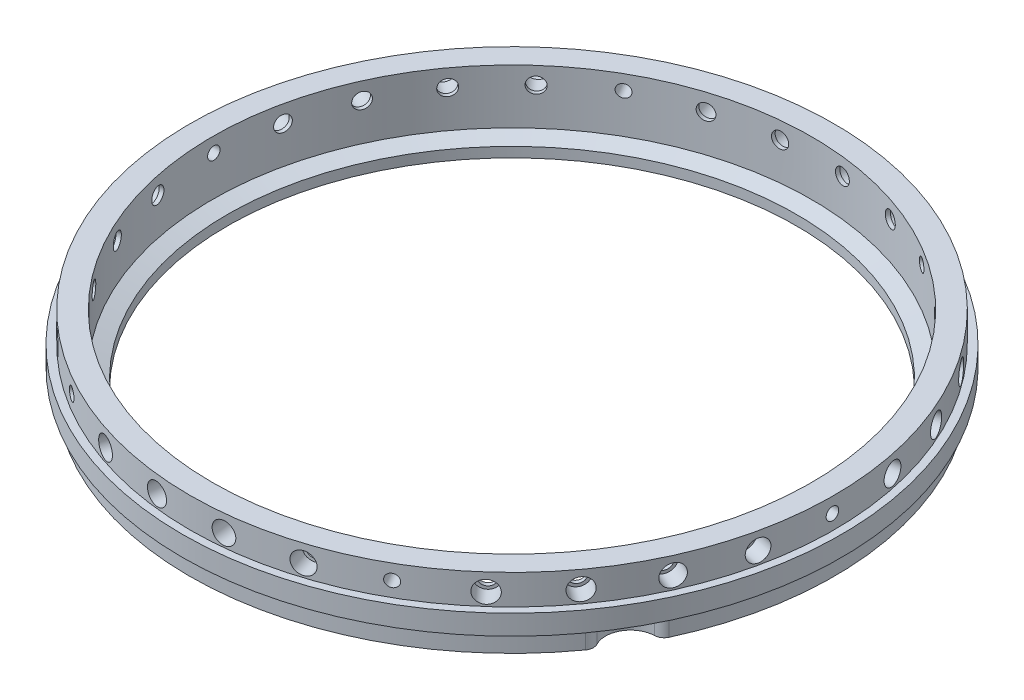
SolidWorks part; units mm, degrees
ref_plane "Front Plane" through (0, 0, 0) normal (0, 0, 1) x (1, 0, 0)
ref_plane "Top Plane" through (0, 0, 0) normal (0, 1, 0) x (1, 0, 0)
ref_plane "Right Plane" through (0, 0, 0) normal (1, 0, 0) x (0, 0, -1)
ref_plane "Plane1" through (0, 0, -36.724) normal (0, 0, 1) x (1, 0, 0)
sketch "Sketch1" plane through (0, 0, -36.724) normal (0, 0, 1) x (1, 0, 0)
  line L0 (122.0725, -167.4149) -> (38.2525, -167.4149)
  line L1 (38.2525, -167.4149) -> (38.2525, -172.4949)
  line L2 (38.2525, -172.4949) -> (122.0725, -172.4949)
  line L3 (122.0725, -172.4949) -> (122.0725, -167.4149)
  line L4 (38.2525, -167.4149) -> (38.2525, -172.4949) construction
revolve "Revolve1" add sketch "Sketch1" angle 360 about L4
sketch "Sketch2" plane through (0, -172.4949, 0) normal (0, -1, 0) x (1, 0, 0)
  arc A0 (-35.7204, -1.3902) -> (-29.763, 9.0403) centre (-34.5321, 4.8476) ccw
  arc A1 (-29.763, 9.0403) -> (105.8389, 9.6716) centre (38.2525, -36.724) cw
  arc A2 (105.8389, 9.6716) -> (111.8933, -0.7029) centre (110.6469, 5.5236) ccw
  arc A3 (111.8933, -0.7029) -> (44.6391, -118.4533) centre (38.2525, -36.724) cw
  arc A4 (44.6391, -118.4533) -> (32.6273, -118.5092) centre (38.6428, -120.5431) ccw
  arc A5 (32.6273, -118.5092) -> (-35.7204, -1.3902) centre (38.2525, -36.724) cw
extrude "Boss-Extrude1" add sketch "Sketch2" along normal blind 5.08
sketch "Sketch3" plane through (0, -167.4149, 0) normal (0, 1, 0) x (-1, 0, 0)
  circle A0 centre (-38.2525, -36.724) radius 81.8896
extrude "Boss-Extrude2" add sketch "Sketch3" along normal blind 7.62
hole_wizard "Hole1" positions "Sketch5" profile "Sketch4" legacy
sketch "Sketch5" plane through (0, -159.7949, 0) normal (0, 1, 0) x (1, 0, 0)
  point P0 (38.2525, 36.724)
sketch "Sketch4" plane through (38.2525, -159.7949, -36.724) normal (1, 0, 0) x (0, 0, 1)
  line L0 (0, 0) -> (0, 17.78)
  line L1 (0, 17.78) -> (72.39, 17.78)
  line L2 (72.39, 17.78) -> (72.39, 15.24)
  line L3 (72.39, 15.24) -> (76.2, 13.8533)
  line L4 (76.2, 13.8533) -> (76.2, 0)
  line L5 (76.2, 0) -> (0, 0)
  line L6 (0, -6.13) -> (0, 109.2824) construction
  line L7 (-72.39, 15.24) -> (-76.2, 13.8533) construction
  line L8 (0, 17.78) -> (-72.39, 17.78) construction
  dimension "Diameter" = 144.78
  dimension "Depth" = 17.78
  dimension "C-Drill Diameter" = 152.4
  dimension "C-Drill Depth" = 13.8533
  dimension "C-Drill Angle" = 140
hole_wizard "CBORE for M3.5 Hex Head Machine Screw1" positions "3DSketch1" profile "Sketch6" counterbore size "M3.5" standard "ANSI Metric"
sketch3d "3DSketch1"
  point P0 (13.3101, -164.1649, -114.7226)
sketch "Sketch6" plane through (13.3101, -164.1649, -114.7226) normal (0, 1, 0) x (-0.9525, 0, 0.3046)
  line L0 (0, 0) -> (0, 5.6896)
  line L1 (0, 5.6896) -> (2, 5.6896)
  line L3 (2, 5.6896) -> (2, 4.6896)
  line L4 (2, 4.6896) -> (2.75, 4.6896)
  line L5 (2.75, 4.6896) -> (2.75, 0)
  line L7 (2.75, 0) -> (0, 0)
  line L11 (0, -6.35) -> (0, 107.95) construction
  dimension "Thru Hole Dia." = 4
  dimension "Thru Hole Depth" = 5.6896
  dimension "C'Bore Dia." = 5.5
  dimension "C'Bore Depth" = 4.6896
hole_wizard "CBORE for M3.5 Hex Head Machine Screw2" positions "3DSketch2" profile "Sketch7" counterbore size "M3.5" standard "ANSI Metric"
sketch3d "3DSketch2"
  point P0 (118.431, -164.1649, -53.3767)
sketch "Sketch7" plane through (118.431, -164.1649, -53.3767) normal (0, 1, 0) x (-0.2034, 0, -0.9791)
  line L0 (0, 0) -> (0, 5.6896)
  line L1 (0, 5.6896) -> (2, 5.6896)
  line L3 (2, 5.6896) -> (2, 4.6896)
  line L4 (2, 4.6896) -> (2.75, 4.6896)
  line L5 (2.75, 4.6896) -> (2.75, 0)
  line L7 (2.75, 0) -> (0, 0)
  line L11 (0, -6.35) -> (0, 107.95) construction
  dimension "Thru Hole Dia." = 4
  dimension "Thru Hole Depth" = 5.6896
  dimension "C'Bore Dia." = 5.5
  dimension "C'Bore Depth" = 4.6896
hole_wizard "CBORE for M3.5 Hex Head Machine Screw3" positions "3DSketch3" profile "Sketch8" counterbore size "M3.5" standard "ANSI Metric"
sketch3d "3DSketch3"
  point P0 (112.9065, -164.1649, -3.0685)
sketch "Sketch8" plane through (112.9065, -164.1649, -3.0685) normal (0, 1, 0) x (0.411, 0, -0.9116)
  line L0 (0, 0) -> (0, 5.6896)
  line L1 (0, 5.6896) -> (2, 5.6896)
  line L3 (2, 5.6896) -> (2, 4.6896)
  line L4 (2, 4.6896) -> (2.75, 4.6896)
  line L5 (2.75, 4.6896) -> (2.75, 0)
  line L7 (2.75, 0) -> (0, 0)
  line L11 (0, -6.35) -> (0, 107.95) construction
  dimension "Thru Hole Dia." = 4
  dimension "Thru Hole Depth" = 5.6896
  dimension "C'Bore Dia." = 5.5
  dimension "C'Bore Depth" = 4.6896
hole_wizard "CBORE for M3.5 Hex Head Machine Screw4" positions "3DSketch4" profile "Sketch9" counterbore size "M3.5" standard "ANSI Metric"
sketch3d "3DSketch4"
  point P0 (118.2725, -164.1649, -19.3254)
sketch "Sketch9" plane through (118.2725, -164.1649, -19.3254) normal (0, 1, 0) x (0.2125, 0, -0.9772)
  line L0 (0, 0) -> (0, 5.6896)
  line L1 (0, 5.6896) -> (2, 5.6896)
  line L3 (2, 5.6896) -> (2, 4.6896)
  line L4 (2, 4.6896) -> (2.75, 4.6896)
  line L5 (2.75, 4.6896) -> (2.75, 0)
  line L7 (2.75, 0) -> (0, 0)
  line L11 (0, -6.35) -> (0, 107.95) construction
  dimension "Thru Hole Dia." = 4
  dimension "Thru Hole Depth" = 5.6896
  dimension "C'Bore Dia." = 5.5
  dimension "C'Bore Depth" = 4.6896
hole_wizard "CBORE for M3.5 Hex Head Machine Screw5" positions "3DSketch5" profile "Sketch10" counterbore size "M3.5" standard "ANSI Metric"
sketch3d "3DSketch5"
  point P0 (47.1914, -164.1649, -118.1242)
sketch "Sketch10" plane through (47.1914, -164.1649, -118.1242) normal (0, 1, 0) x (-0.994, 0, -0.1092)
  line L0 (0, 0) -> (0, 5.6896)
  line L1 (0, 5.6896) -> (2, 5.6896)
  line L3 (2, 5.6896) -> (2, 4.6896)
  line L4 (2, 4.6896) -> (2.75, 4.6896)
  line L5 (2.75, 4.6896) -> (2.75, 0)
  line L7 (2.75, 0) -> (0, 0)
  line L11 (0, -6.35) -> (0, 107.95) construction
  dimension "Thru Hole Dia." = 4
  dimension "Thru Hole Depth" = 5.6896
  dimension "C'Bore Dia." = 5.5
  dimension "C'Bore Depth" = 4.6896
hole_wizard "CBORE for M3.5 Hex Head Machine Screw6" positions "3DSketch6" profile "Sketch11" counterbore size "M3.5" standard "ANSI Metric"
sketch3d "3DSketch6"
  point P0 (30.072, -164.1649, -118.2039)
sketch "Sketch11" plane through (30.072, -164.1649, -118.2039) normal (0, 1, 0) x (-0.995, 0, 0.0999)
  line L0 (0, 0) -> (0, 5.6896)
  line L1 (0, 5.6896) -> (2, 5.6896)
  line L3 (2, 5.6896) -> (2, 4.6896)
  line L4 (2, 4.6896) -> (2.75, 4.6896)
  line L5 (2.75, 4.6896) -> (2.75, 0)
  line L7 (2.75, 0) -> (0, 0)
  line L11 (0, -6.35) -> (0, 107.95) construction
  dimension "Thru Hole Dia." = 4
  dimension "Thru Hole Depth" = 5.6896
  dimension "C'Bore Dia." = 5.5
  dimension "C'Bore Depth" = 4.6896
hole_wizard "CBORE for M3.5 Hex Head Machine Screw7" positions "3DSketch7" profile "Sketch12" counterbore size "M3.5" standard "ANSI Metric"
sketch3d "3DSketch7"
  point P0 (104.726, -164.1649, -84.5485)
sketch "Sketch12" plane through (104.726, -164.1649, -84.5485) normal (0, 1, 0) x (-0.584, 0, -0.8117)
  line L0 (0, 0) -> (0, 5.6896)
  line L1 (0, 5.6896) -> (2, 5.6896)
  line L3 (2, 5.6896) -> (2, 4.6896)
  line L4 (2, 4.6896) -> (2.75, 4.6896)
  line L5 (2.75, 4.6896) -> (2.75, 0)
  line L7 (2.75, 0) -> (0, 0)
  line L11 (0, -6.35) -> (0, 107.95) construction
  dimension "Thru Hole Dia." = 4
  dimension "Thru Hole Depth" = 5.6896
  dimension "C'Bore Dia." = 5.5
  dimension "C'Bore Depth" = 4.6896
hole_wizard "CBORE for M3.5 Hex Head Machine Screw8" positions "3DSketch8" profile "Sketch13" counterbore size "M3.5" standard "ANSI Metric"
sketch3d "3DSketch8"
  point P0 (63.9201, -164.1649, -114.4869)
sketch "Sketch13" plane through (63.9201, -164.1649, -114.4869) normal (0, 1, 0) x (-0.9496, 0, -0.3134)
  line L0 (0, 0) -> (0, 5.6896)
  line L1 (0, 5.6896) -> (2, 5.6896)
  line L3 (2, 5.6896) -> (2, 4.6896)
  line L4 (2, 4.6896) -> (2.75, 4.6896)
  line L5 (2.75, 4.6896) -> (2.75, 0)
  line L7 (2.75, 0) -> (0, 0)
  line L11 (0, -6.35) -> (0, 107.95) construction
  dimension "Thru Hole Dia." = 4
  dimension "Thru Hole Depth" = 5.6896
  dimension "C'Bore Dia." = 5.5
  dimension "C'Bore Depth" = 4.6896
hole_wizard "Hole2" positions "3DSketch9" profile "Sketch14" legacy
sketch3d "3DSketch9"
  point P0 (-2.3617, -163.6049, -107.8323)
sketch "Sketch14" plane through (-2.3617, -163.6049, -107.8323) normal (0, 1, 0) x (-0.8683, 0, 0.496)
  line L0 (0, 0) -> (0, 169.4853)
  line L1 (0, 169.4853) -> (1.5875, 169.4853)
  line L2 (1.5875, 169.4853) -> (1.5875, 0)
  line L3 (1.5875, 0) -> (0, 0)
  line L4 (0, 110) -> (0, -10) construction
  dimension "Diameter" = 3.175
  dimension "Depth" = 169.4853
hole_wizard "CBORE for M3.5 Hex Head Machine Screw9" positions "3DSketch10" profile "Sketch15" counterbore size "M3.5" standard "ANSI Metric"
sketch3d "3DSketch10"
  point P0 (93.3301, -164.1649, -97.324)
sketch "Sketch15" plane through (93.3301, -164.1649, -97.324) normal (0, 1, 0) x (-0.74, 0, -0.6726)
  line L0 (0, 0) -> (0, 5.6896)
  line L1 (0, 5.6896) -> (2, 5.6896)
  line L3 (2, 5.6896) -> (2, 4.6896)
  line L4 (2, 4.6896) -> (2.75, 4.6896)
  line L5 (2.75, 4.6896) -> (2.75, 0)
  line L7 (2.75, 0) -> (0, 0)
  line L11 (0, -6.35) -> (0, 107.95) construction
  dimension "Thru Hole Dia." = 4
  dimension "Thru Hole Depth" = 5.6896
  dimension "C'Bore Dia." = 5.5
  dimension "C'Bore Depth" = 4.6896
ref_plane "Plane2" through (114.2633, 0, 0.532) normal (-1, 0, -0.0047) x (-0.0047, 0, 1)
hole_wizard "Hole3" positions "Sketch17" profile "Sketch16" legacy
sketch "Sketch17" plane through (114.2633, 0, 0.532) normal (-1, 0, -0.0047) x (-0.0047, 0, 1)
  point P0 (-36.9017, -163.6049)
sketch "Sketch16" plane through (114.4352, -163.6049, -36.3693) normal (0, 1, 0) x (-0.0047, 0, 1)
  line L0 (0, 0) -> (0, 8.0259)
  line L1 (0, 8.0259) -> (1.5875, 8.0259)
  line L2 (1.5875, 8.0259) -> (1.5875, 0)
  line L3 (1.5875, 0) -> (0, 0)
  line L4 (0, 110) -> (0, -10) construction
  dimension "Diameter" = 3.175
  dimension "Depth" = 8.0259
hole_wizard "CBORE for M3.5 Hex Head Machine Screw10" positions "3DSketch11" profile "Sketch18" counterbore size "M3.5" standard "ANSI Metric"
sketch3d "3DSketch11"
  point P0 (104.2778, -164.1649, 11.7175)
sketch "Sketch18" plane through (104.2778, -164.1649, 11.7175) normal (0, 1, 0) x (0.5915, 0, -0.8063)
  line L0 (0, 0) -> (0, 5.6896)
  line L1 (0, 5.6896) -> (2, 5.6896)
  line L3 (2, 5.6896) -> (2, 4.6896)
  line L4 (2, 4.6896) -> (2.75, 4.6896)
  line L5 (2.75, 4.6896) -> (2.75, 0)
  line L7 (2.75, 0) -> (0, 0)
  line L11 (0, -6.35) -> (0, 107.95) construction
  dimension "Thru Hole Dia." = 4
  dimension "Thru Hole Depth" = 5.6896
  dimension "C'Bore Dia." = 5.5
  dimension "C'Bore Depth" = 4.6896
hole_wizard "CBORE for M3.5 Hex Head Machine Screw11" positions "3DSketch12" profile "Sketch19" counterbore size "M3.5" standard "ANSI Metric"
sketch3d "3DSketch12"
  point P0 (113.2167, -164.1649, -69.6828)
sketch "Sketch19" plane through (113.2167, -164.1649, -69.6828) normal (0, 1, 0) x (-0.4025, 0, -0.9154)
  line L0 (0, 0) -> (0, 5.6896)
  line L1 (0, 5.6896) -> (2, 5.6896)
  line L3 (2, 5.6896) -> (2, 4.6896)
  line L4 (2, 4.6896) -> (2.75, 4.6896)
  line L5 (2.75, 4.6896) -> (2.75, 0)
  line L7 (2.75, 0) -> (0, 0)
  line L11 (0, -6.35) -> (0, 107.95) construction
  dimension "Thru Hole Dia." = 4
  dimension "Thru Hole Depth" = 5.6896
  dimension "C'Bore Dia." = 5.5
  dimension "C'Bore Depth" = 4.6896
hole_wizard "CBORE for M3.5 Hex Head Machine Screw12" positions "3DSketch13" profile "Sketch20" counterbore size "M3.5" standard "ANSI Metric"
sketch3d "3DSketch13"
  point P0 (92.7634, -164.1649, 24.3863)
sketch "Sketch20" plane through (92.7634, -164.1649, 24.3863) normal (0, 1, 0) x (0.7463, 0, -0.6657)
  line L0 (0, 0) -> (0, 5.6896)
  line L1 (0, 5.6896) -> (2, 5.6896)
  line L3 (2, 5.6896) -> (2, 4.6896)
  line L4 (2, 4.6896) -> (2.75, 4.6896)
  line L5 (2.75, 4.6896) -> (2.75, 0)
  line L7 (2.75, 0) -> (0, 0)
  line L11 (0, -6.35) -> (0, 107.95) construction
  dimension "Thru Hole Dia." = 4
  dimension "Thru Hole Depth" = 5.6896
  dimension "C'Bore Dia." = 5.5
  dimension "C'Bore Depth" = 4.6896
hole_wizard "CBORE for M3.5 Hex Head Machine Screw13" positions "3DSketch14" profile "Sketch21" counterbore size "M3.5" standard "ANSI Metric"
sketch3d "3DSketch14"
  point P0 (-16.2584, -164.1649, -97.8342)
sketch "Sketch21" plane through (-16.2584, -164.1649, -97.8342) normal (0, 1, 0) x (-0.7463, 0, 0.6657)
  line L0 (0, 0) -> (0, 200.2364)
  line L1 (0, 200.2364) -> (2, 200.2364)
  line L3 (2, 200.2364) -> (2, 4.6896)
  line L4 (2, 4.6896) -> (2.75, 4.6896)
  line L5 (2.75, 4.6896) -> (2.75, 0)
  line L7 (2.75, 0) -> (0, 0)
  line L11 (0, -6.35) -> (0, 107.95) construction
  dimension "Thru Hole Dia." = 4
  dimension "Thru Hole Depth" = 200.2364
  dimension "C'Bore Dia." = 5.5
  dimension "C'Bore Depth" = 4.6896
hole_wizard "CBORE for M3.5 Hex Head Machine Screw14" positions "3DSketch15" profile "Sketch22" counterbore size "M3.5" standard "ANSI Metric"
sketch3d "3DSketch15"
  point P0 (-27.7727, -164.1649, -85.1654)
sketch "Sketch22" plane through (-27.7727, -164.1649, -85.1654) normal (0, 1, 0) x (-0.5915, 0, 0.8063)
  line L0 (0, 0) -> (0, 199.0546)
  line L1 (0, 199.0546) -> (2, 199.0546)
  line L3 (2, 199.0546) -> (2, 4.6896)
  line L4 (2, 4.6896) -> (2.75, 4.6896)
  line L5 (2.75, 4.6896) -> (2.75, 0)
  line L7 (2.75, 0) -> (0, 0)
  line L11 (0, -6.35) -> (0, 107.95) construction
  dimension "Thru Hole Dia." = 4
  dimension "Thru Hole Depth" = 199.0546
  dimension "C'Bore Dia." = 5.5
  dimension "C'Bore Depth" = 4.6896
hole_wizard "CBORE for M3.5 Hex Head Machine Screw15" positions "3DSketch16" profile "Sketch23" counterbore size "M3.5" standard "ANSI Metric"
sketch3d "3DSketch16"
  point P0 (-28.2209, -164.1649, 11.1006)
sketch "Sketch23" plane through (-28.2209, -164.1649, 11.1006) normal (0, 1, 0) x (0.584, 0, 0.8117)
  line L0 (0, 0) -> (0, 198.882)
  line L1 (0, 198.882) -> (2, 198.882)
  line L3 (2, 198.882) -> (2, 4.6896)
  line L4 (2, 4.6896) -> (2.75, 4.6896)
  line L5 (2.75, 4.6896) -> (2.75, 0)
  line L7 (2.75, 0) -> (0, 0)
  line L11 (0, -6.35) -> (0, 107.95) construction
  dimension "Thru Hole Dia." = 4
  dimension "Thru Hole Depth" = 198.882
  dimension "C'Bore Dia." = 5.5
  dimension "C'Bore Depth" = 4.6896
hole_wizard "CBORE for M3.5 Hex Head Machine Screw16" positions "3DSketch17" profile "Sketch24" counterbore size "M3.5" standard "ANSI Metric"
sketch3d "3DSketch17"
  point P0 (-36.4015, -164.1649, -70.3794)
sketch "Sketch24" plane through (-36.4015, -164.1649, -70.3794) normal (0, 1, 0) x (-0.411, 0, 0.9116)
  line L0 (0, 0) -> (0, 192.7522)
  line L1 (0, 192.7522) -> (2, 192.7522)
  line L3 (2, 192.7522) -> (2, 4.6896)
  line L4 (2, 4.6896) -> (2.75, 4.6896)
  line L5 (2.75, 4.6896) -> (2.75, 0)
  line L7 (2.75, 0) -> (0, 0)
  line L11 (0, -6.35) -> (0, 107.95) construction
  dimension "Thru Hole Dia." = 4
  dimension "Thru Hole Depth" = 192.7522
  dimension "C'Bore Dia." = 5.5
  dimension "C'Bore Depth" = 4.6896
hole_wizard "CBORE for M3.5 Hex Head Machine Screw17" positions "3DSketch18" profile "Sketch25" counterbore size "M3.5" standard "ANSI Metric"
sketch3d "3DSketch18"
  point P0 (-36.7116, -164.1649, -3.7651)
sketch "Sketch25" plane through (-36.7116, -164.1649, -3.7651) normal (0, 1, 0) x (0.4025, 0, 0.9154)
  line L0 (0, 0) -> (0, 192.3567)
  line L1 (0, 192.3567) -> (2, 192.3567)
  line L3 (2, 192.3567) -> (2, 4.6896)
  line L4 (2, 4.6896) -> (2.75, 4.6896)
  line L5 (2.75, 4.6896) -> (2.75, 0)
  line L7 (2.75, 0) -> (0, 0)
  line L11 (0, -6.35) -> (0, 107.95) construction
  dimension "Thru Hole Dia." = 4
  dimension "Thru Hole Depth" = 192.3567
  dimension "C'Bore Dia." = 5.5
  dimension "C'Bore Depth" = 4.6896
hole_wizard "CBORE for M3.5 Hex Head Machine Screw18" positions "3DSketch19" profile "Sketch26" counterbore size "M3.5" standard "ANSI Metric"
sketch3d "3DSketch19"
  point P0 (12.5849, -164.1649, 41.039)
sketch "Sketch26" plane through (12.5849, -164.1649, 41.039) normal (0, 1, 0) x (0.9496, 0, 0.3134)
  line L0 (0, 0) -> (0, 187.7584)
  line L1 (0, 187.7584) -> (2, 187.7584)
  line L3 (2, 187.7584) -> (2, 4.6896)
  line L4 (2, 4.6896) -> (2.75, 4.6896)
  line L5 (2.75, 4.6896) -> (2.75, 0)
  line L7 (2.75, 0) -> (0, 0)
  line L11 (0, -6.35) -> (0, 107.95) construction
  dimension "Thru Hole Dia." = 4
  dimension "Thru Hole Depth" = 187.7584
  dimension "C'Bore Dia." = 5.5
  dimension "C'Bore Depth" = 4.6896
hole_wizard "CBORE for M3.5 Hex Head Machine Screw19" positions "3DSketch20" profile "Sketch27" counterbore size "M3.5" standard "ANSI Metric"
sketch3d "3DSketch20"
  point P0 (-41.7675, -164.1649, -54.1225)
sketch "Sketch27" plane through (-41.7675, -164.1649, -54.1225) normal (0, 1, 0) x (-0.2125, 0, 0.9772)
  line L0 (0, 0) -> (0, 181.6046)
  line L1 (0, 181.6046) -> (2, 181.6046)
  line L3 (2, 181.6046) -> (2, 4.6896)
  line L4 (2, 4.6896) -> (2.75, 4.6896)
  line L5 (2.75, 4.6896) -> (2.75, 0)
  line L7 (2.75, 0) -> (0, 0)
  line L11 (0, -6.35) -> (0, 107.95) construction
  dimension "Thru Hole Dia." = 4
  dimension "Thru Hole Depth" = 181.6046
  dimension "C'Bore Dia." = 5.5
  dimension "C'Bore Depth" = 4.6896
hole_wizard "CBORE for M3.5 Hex Head Machine Screw20" positions "3DSketch21" profile "Sketch28" counterbore size "M3.5" standard "ANSI Metric"
sketch3d "3DSketch21"
  point P0 (63.1949, -164.1649, 41.2746)
sketch "Sketch28" plane through (63.1949, -164.1649, 41.2746) normal (0, 1, 0) x (0.9525, 0, -0.3046)
  line L0 (0, 0) -> (0, 187.2573)
  line L1 (0, 187.2573) -> (2, 187.2573)
  line L3 (2, 187.2573) -> (2, 4.6896)
  line L4 (2, 4.6896) -> (2.75, 4.6896)
  line L5 (2.75, 4.6896) -> (2.75, 0)
  line L7 (2.75, 0) -> (0, 0)
  line L11 (0, -6.35) -> (0, 107.95) construction
  dimension "Thru Hole Dia." = 4
  dimension "Thru Hole Depth" = 187.2573
  dimension "C'Bore Dia." = 5.5
  dimension "C'Bore Depth" = 4.6896
hole_wizard "CBORE for M3.5 Hex Head Machine Screw21" positions "3DSketch22" profile "Sketch29" counterbore size "M3.5" standard "ANSI Metric"
sketch3d "3DSketch22"
  point P0 (-41.926, -164.1649, -20.0713)
sketch "Sketch29" plane through (-41.926, -164.1649, -20.0713) normal (0, 1, 0) x (0.2034, 0, 0.9791)
  line L0 (0, 0) -> (0, 181.0034)
  line L1 (0, 181.0034) -> (2, 181.0034)
  line L3 (2, 181.0034) -> (2, 4.6896)
  line L4 (2, 4.6896) -> (2.75, 4.6896)
  line L5 (2.75, 4.6896) -> (2.75, 0)
  line L7 (2.75, 0) -> (0, 0)
  line L11 (0, -6.35) -> (0, 107.95) construction
  dimension "Thru Hole Dia." = 4
  dimension "Thru Hole Depth" = 181.0034
  dimension "C'Bore Dia." = 5.5
  dimension "C'Bore Depth" = 4.6896
hole_wizard "CBORE for M3.5 Hex Head Machine Screw22" positions "3DSketch23" profile "Sketch30" counterbore size "M3.5" standard "ANSI Metric"
sketch3d "3DSketch23"
  point P0 (29.3136, -164.1649, 44.6763)
sketch "Sketch30" plane through (29.3136, -164.1649, 44.6763) normal (0, 1, 0) x (0.994, 0, 0.1092)
  line L0 (0, 0) -> (0, 174.3583)
  line L1 (0, 174.3583) -> (2, 174.3583)
  line L3 (2, 174.3583) -> (2, 4.6896)
  line L4 (2, 4.6896) -> (2.75, 4.6896)
  line L5 (2.75, 4.6896) -> (2.75, 0)
  line L7 (2.75, 0) -> (0, 0)
  line L11 (0, -6.35) -> (0, 107.95) construction
  dimension "Thru Hole Dia." = 4
  dimension "Thru Hole Depth" = 174.3583
  dimension "C'Bore Dia." = 5.5
  dimension "C'Bore Depth" = 4.6896
hole_wizard "CBORE for M3.5 Hex Head Machine Screw23" positions "3DSketch24" profile "Sketch31" counterbore size "M3.5" standard "ANSI Metric"
sketch3d "3DSketch24"
  point P0 (46.433, -164.1649, 44.756)
sketch "Sketch31" plane through (46.433, -164.1649, 44.756) normal (0, 1, 0) x (0.995, 0, -0.0999)
  line L0 (0, 0) -> (0, 173.6637)
  line L1 (0, 173.6637) -> (2, 173.6637)
  line L3 (2, 173.6637) -> (2, 4.6896)
  line L4 (2, 4.6896) -> (2.75, 4.6896)
  line L5 (2.75, 4.6896) -> (2.75, 0)
  line L7 (2.75, 0) -> (0, 0)
  line L11 (0, -6.35) -> (0, 107.95) construction
  dimension "Thru Hole Dia." = 4
  dimension "Thru Hole Depth" = 173.6637
  dimension "C'Bore Dia." = 5.5
  dimension "C'Bore Depth" = 4.6896
hole_wizard "Hole4" positions "3DSketch25" profile "Sketch32" legacy
sketch3d "3DSketch25"
  point P0 (-3.022, -163.6049, 34.0031)
sketch "Sketch32" plane through (-3.022, -163.6049, 34.0031) normal (0, 1, 0) x (0.8637, 0, 0.504)
  line L0 (0, 0) -> (0, 163.7792)
  line L1 (0, 163.7792) -> (1.5875, 163.7792)
  line L2 (1.5875, 163.7792) -> (1.5875, 0)
  line L3 (1.5875, 0) -> (0, 0)
  line L4 (0, 110) -> (0, -10) construction
  dimension "Diameter" = 3.175
  dimension "Depth" = 163.7792
ref_plane "Plane3" through (-38.1019, 0, -0.1774) normal (1, 0, 0.0047) x (0.0047, 0, -1)
hole_wizard "Hole5" positions "Sketch34" profile "Sketch33" legacy
sketch "Sketch34" plane through (-38.1019, 0, -0.1774) normal (1, 0, 0.0047) x (0.0047, 0, -1)
  point P0 (36.9017, -163.6049)
sketch "Sketch33" plane through (-37.9301, -163.6049, -37.0787) normal (0, 1, 0) x (0.0047, 0, -1)
  line L0 (0, 0) -> (0, 8.0259)
  line L1 (0, 8.0259) -> (1.5875, 8.0259)
  line L2 (1.5875, 8.0259) -> (1.5875, 0)
  line L3 (1.5875, 0) -> (0, 0)
  line L4 (0, 110) -> (0, -10) construction
  dimension "Diameter" = 3.175
  dimension "Depth" = 8.0259
hole_wizard "CBORE for M3.5 Hex Head Machine Screw24" positions "3DSketch26" profile "Sketch35" counterbore size "M3.5" standard "ANSI Metric"
sketch3d "3DSketch26"
  point P0 (-16.8251, -164.1649, 23.8761)
sketch "Sketch35" plane through (-16.8251, -164.1649, 23.8761) normal (0, 1, 0) x (0.74, 0, 0.6726)
  line L0 (0, 0) -> (0, 200.2941)
  line L1 (0, 200.2941) -> (2, 200.2941)
  line L3 (2, 200.2941) -> (2, 4.6896)
  line L4 (2, 4.6896) -> (2.75, 4.6896)
  line L5 (2.75, 4.6896) -> (2.75, 0)
  line L7 (2.75, 0) -> (0, 0)
  line L11 (0, -6.35) -> (0, 107.95) construction
  dimension "Thru Hole Dia." = 4
  dimension "Thru Hole Depth" = 200.2941
  dimension "C'Bore Dia." = 5.5
  dimension "C'Bore Depth" = 4.6896
fillet "Fillet1" radius 2.54 6 edges at (111.8933, -175.0349, -0.7029) (32.6273, -175.0349, -118.5092) (44.6391, -175.0349, -118.4533) (-29.763, -175.0349, 9.0403) (-35.7204, -175.0349, -1.3902) (105.8389, -175.0349, 9.6716)
